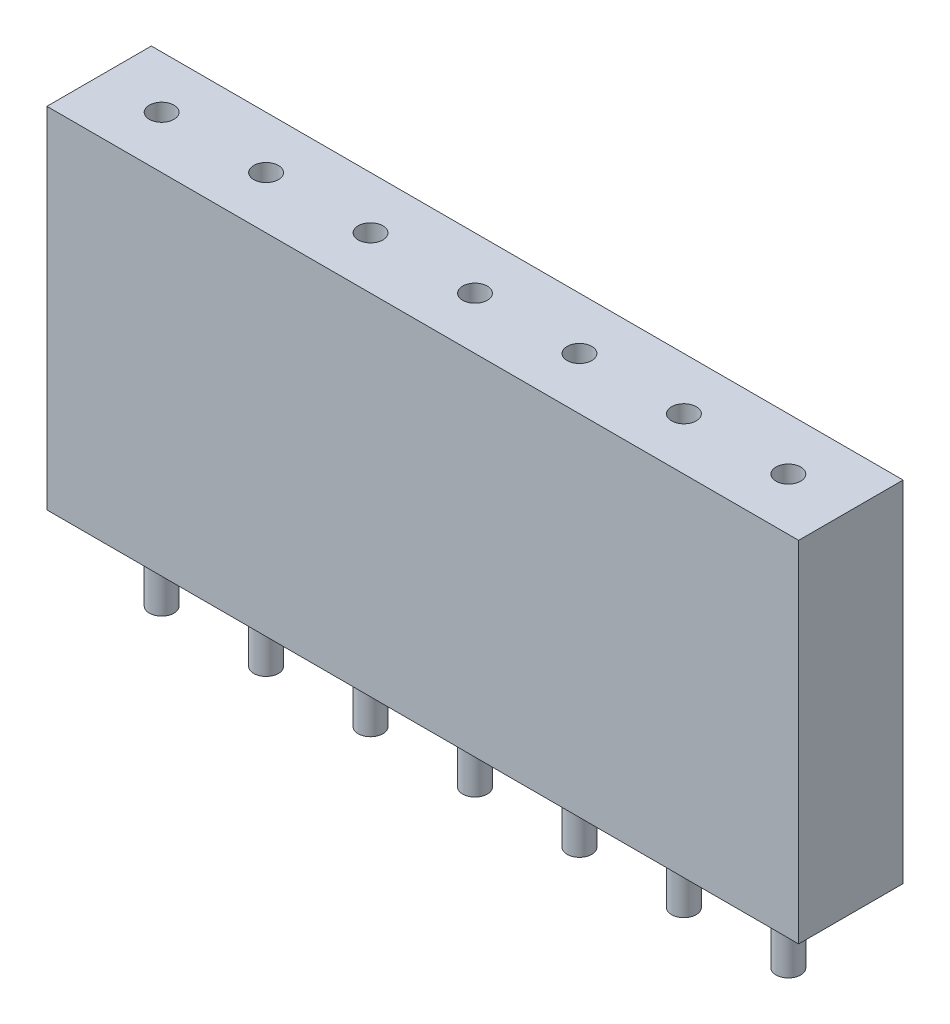
SolidWorks part; units mm, degrees
ref_plane "Спереди" through (0, 0, 0) normal (0, 0, 1) x (1, 0, 0)
ref_plane "Сверху" through (0, 0, 0) normal (0, 1, 0) x (1, 0, 0)
ref_plane "Справа" through (0, 0, 0) normal (1, 0, 0) x (0, 0, -1)
sketch "Эскиз1" plane through (0, 0, 0) normal (0, 1, 0) x (1, 0, 0)
  line L1 (-9.14, 1.27) -> (9.14, 1.27)
  line L2 (-9.14, 1.27) -> (-9.14, -1.27)
  line L3 (-9.14, -1.27) -> (9.14, -1.27)
  line L4 (9.14, 1.27) -> (9.14, -1.27)
  line L5 (-9.14, 1.27) -> (9.14, -1.27) construction
  line L6 (-9.14, -1.27) -> (9.14, 1.27) construction
  point P0 (0, 0)
extrude "Бобышка-Вытянуть1" add sketch "Эскиз1" along normal blind 8.5
sketch "Эскиз2" plane through (0, 8.5, 0) normal (0, 1, 0) x (1, 0, 0)
  circle A0 centre (-7.62, 0) radius 0.3
  circle A1 centre (-5.08, 0) radius 0.3
  circle A2 centre (-2.54, 0) radius 0.3
  circle A3 centre (0, 0) radius 0.3
  circle A4 centre (2.54, 0) radius 0.3
  circle A5 centre (5.08, 0) radius 0.3
  circle A6 centre (7.62, 0) radius 0.3
  dimension "D1" = 7
extrude "Вырез-Вытянуть1" cut sketch "Эскиз2" against normal blind 8.5
sketch "Эскиз3" plane through (0, 0, 0) normal (0, -1, 0) x (1, 0, 0)
  circle A0 centre (-7.62, 0) radius 0.3
  circle A1 centre (-5.08, 0) radius 0.3
  circle A2 centre (-2.54, 0) radius 0.3
  circle A3 centre (0, 0) radius 0.3
  circle A4 centre (2.54, 0) radius 0.3
  circle A5 centre (5.08, 0) radius 0.3
  circle A6 centre (7.62, 0) radius 0.3
  dimension "D1" = 7
extrude "Бобышка-Вытянуть2" add sketch "Эскиз3" along normal blind 1.9 separate body
ref_plane "Плоскость1" through (0, 0, 0) normal (0, 0, 1) x (1, 0, 0)
